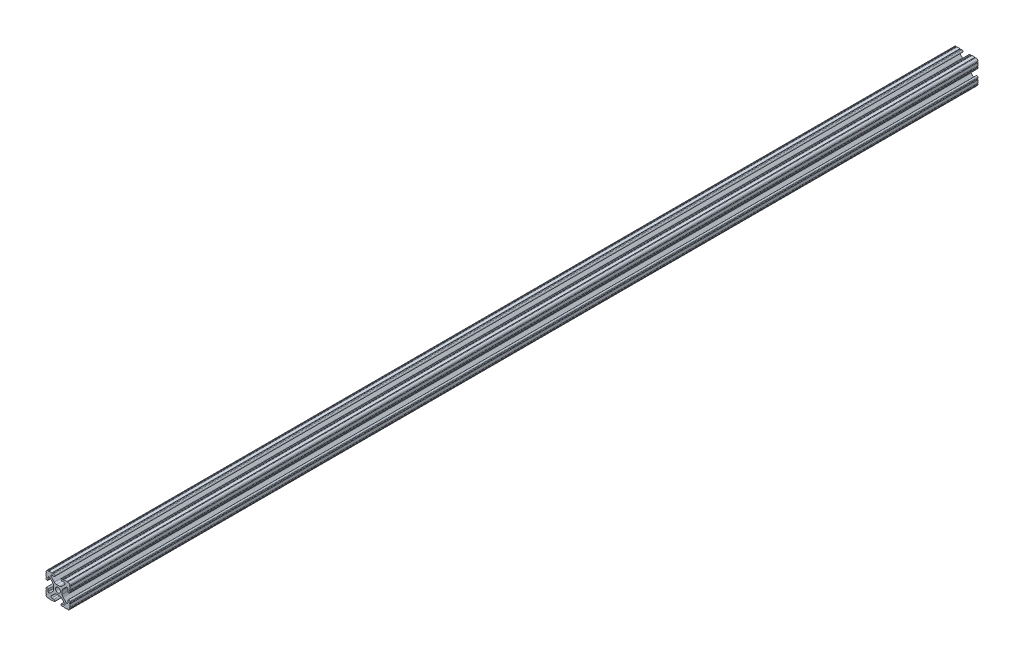
SolidWorks part; units mm, degrees
material "6061-T6 (SS)"
ref_plane "Front Plane" through (0, 0, 0) normal (0, 0, 1) x (1, 0, 0)
ref_plane "Top Plane" through (0, 0, 0) normal (0, 1, 0) x (1, 0, 0)
ref_plane "Right Plane" through (0, 0, 0) normal (1, 0, 0) x (0, 0, -1)
ref_plane "Plane1" through (0, 0, -450.85) normal (0, 0, -1) x (-1, 0, 0)
sketch "Sketch1" plane through (0, 0, -450.85) normal (0, 0, -1) x (-1, 0, 0)
  line L0 (12.7, -9.5504) -> (12.7, -6.3331)
  line L1 (12.7, -5.3171) -> (12.7, -4.3434)
  line L2 (10.4902, -4.3434) -> (10.4902, -6.4748)
  line L3 (8.7558, -7.1932) -> (5.4257, -3.8632)
  line L4 (4.4958, -1.6181) -> (4.4958, 1.6181)
  line L5 (5.4257, 3.8632) -> (8.7558, 7.1932)
  line L6 (10.4902, 6.4748) -> (10.4902, 4.3434)
  line L7 (12.7, 4.3434) -> (12.7, 5.3171)
  line L8 (12.7, 6.3331) -> (12.7, 9.5504)
  line L9 (9.5504, 12.7) -> (6.3331, 12.7)
  line L10 (5.3171, 12.7) -> (4.3434, 12.7)
  line L11 (4.3434, 10.4902) -> (6.4748, 10.4902)
  line L12 (7.1932, 8.7558) -> (3.8632, 5.4257)
  line L13 (1.6181, 4.4958) -> (-1.6181, 4.4958)
  line L14 (-3.8632, 5.4257) -> (-7.1932, 8.7558)
  line L15 (-6.4748, 10.4902) -> (-4.3434, 10.4902)
  line L16 (-4.3434, 12.7) -> (-5.3171, 12.7)
  line L17 (-6.3331, 12.7) -> (-9.5504, 12.7)
  line L18 (-12.7, 9.5504) -> (-12.7, 6.3331)
  line L19 (-12.7, 5.3171) -> (-12.7, 4.3434)
  line L20 (-10.4902, 4.3434) -> (-10.4902, 6.4748)
  line L21 (-8.7558, 7.1932) -> (-5.4257, 3.8632)
  line L22 (-4.4958, 1.6181) -> (-4.4958, -1.6181)
  line L23 (-5.4257, -3.8632) -> (-8.7558, -7.1932)
  line L24 (-10.4902, -6.4748) -> (-10.4902, -4.3434)
  line L25 (-12.7, -4.3434) -> (-12.7, -5.3171)
  line L26 (-12.7, -6.3331) -> (-12.7, -9.5504)
  line L27 (-9.5504, -12.7) -> (-6.3331, -12.7)
  line L28 (-5.3171, -12.7) -> (-4.3434, -12.7)
  line L29 (-4.3434, -10.4902) -> (-6.4748, -10.4902)
  line L30 (-7.1932, -8.7558) -> (-3.8632, -5.4257)
  line L31 (-1.6181, -4.4958) -> (1.6181, -4.4958)
  line L32 (3.8632, -5.4257) -> (7.1932, -8.7558)
  line L33 (6.4748, -10.4902) -> (4.3434, -10.4902)
  line L34 (4.3434, -12.7) -> (5.3171, -12.7)
  line L35 (6.3331, -12.7) -> (9.5504, -12.7)
  arc A0 (12.6998, -10.5664) -> (12.7, -9.5504) centre (12.7, -10.0584) cw
  arc A1 (12.7, -6.3331) -> (12.7, -5.3171) centre (12.7, -5.8251) cw
  arc A2 (12.7, -4.3434) -> (10.4902, -4.3434) centre (11.5951, -4.3434) ccw
  arc A3 (10.4902, -6.4748) -> (8.7558, -7.1932) centre (9.4742, -6.4748) cw
  arc A4 (5.4257, -3.8632) -> (4.4958, -1.6181) centre (7.6708, -1.6181) cw
  arc A5 (4.4958, 1.6181) -> (5.4257, 3.8632) centre (7.6708, 1.6181) cw
  arc A6 (8.7558, 7.1932) -> (10.4902, 6.4748) centre (9.4742, 6.4748) cw
  arc A7 (10.4902, 4.3434) -> (12.7, 4.3434) centre (11.5951, 4.3434) ccw
  arc A8 (12.7, 5.3171) -> (12.7, 6.3331) centre (12.7, 5.8251) cw
  arc A9 (12.7, 9.5504) -> (12.6998, 10.5664) centre (12.7, 10.0584) cw
  arc A10 (12.6998, 10.5664) -> (10.5664, 12.6998) centre (10.5918, 10.5918) ccw
  arc A11 (10.5664, 12.6998) -> (9.5504, 12.7) centre (10.0584, 12.7) cw
  arc A12 (6.3331, 12.7) -> (5.3171, 12.7) centre (5.8251, 12.7) cw
  arc A13 (4.3434, 12.7) -> (4.3434, 10.4902) centre (4.3434, 11.5951) ccw
  arc A14 (6.4748, 10.4902) -> (7.1932, 8.7558) centre (6.4748, 9.4742) cw
  arc A15 (3.8632, 5.4257) -> (1.6181, 4.4958) centre (1.6181, 7.6708) cw
  arc A16 (-1.6181, 4.4958) -> (-3.8632, 5.4257) centre (-1.6181, 7.6708) cw
  arc A17 (-7.1932, 8.7558) -> (-6.4748, 10.4902) centre (-6.4748, 9.4742) cw
  arc A18 (-4.3434, 10.4902) -> (-4.3434, 12.7) centre (-4.3434, 11.5951) ccw
  arc A19 (-5.3171, 12.7) -> (-6.3331, 12.7) centre (-5.8251, 12.7) cw
  arc A20 (-9.5504, 12.7) -> (-10.5664, 12.6998) centre (-10.0584, 12.7) cw
  arc A21 (-10.5664, 12.6998) -> (-12.6998, 10.5664) centre (-10.5918, 10.5918) ccw
  arc A22 (-12.6998, 10.5664) -> (-12.7, 9.5504) centre (-12.7, 10.0584) cw
  arc A23 (-12.7, 6.3331) -> (-12.7, 5.3171) centre (-12.7, 5.8251) cw
  arc A24 (-12.7, 4.3434) -> (-10.4902, 4.3434) centre (-11.5951, 4.3434) ccw
  arc A25 (-10.4902, 6.4748) -> (-8.7558, 7.1932) centre (-9.4742, 6.4748) cw
  arc A26 (-5.4257, 3.8632) -> (-4.4958, 1.6181) centre (-7.6708, 1.6181) cw
  arc A27 (-4.4958, -1.6181) -> (-5.4257, -3.8632) centre (-7.6708, -1.6181) cw
  arc A28 (-8.7558, -7.1932) -> (-10.4902, -6.4748) centre (-9.4742, -6.4748) cw
  arc A29 (-10.4902, -4.3434) -> (-12.7, -4.3434) centre (-11.5951, -4.3434) ccw
  arc A30 (-12.7, -5.3171) -> (-12.7, -6.3331) centre (-12.7, -5.8251) cw
  arc A31 (-12.7, -9.5504) -> (-12.6998, -10.5664) centre (-12.7, -10.0584) cw
  arc A32 (-12.6998, -10.5664) -> (-10.5664, -12.6998) centre (-10.5918, -10.5918) ccw
  arc A33 (-10.5664, -12.6998) -> (-9.5504, -12.7) centre (-10.0584, -12.7) cw
  arc A34 (-6.3331, -12.7) -> (-5.3171, -12.7) centre (-5.8251, -12.7) cw
  arc A35 (-4.3434, -12.7) -> (-4.3434, -10.4902) centre (-4.3434, -11.5951) ccw
  arc A36 (-6.4748, -10.4902) -> (-7.1932, -8.7558) centre (-6.4748, -9.4742) cw
  arc A37 (-3.8632, -5.4257) -> (-1.6181, -4.4958) centre (-1.6181, -7.6708) cw
  arc A38 (1.6181, -4.4958) -> (3.8632, -5.4257) centre (1.6181, -7.6708) cw
  arc A39 (7.1932, -8.7558) -> (6.4748, -10.4902) centre (6.4748, -9.4742) cw
  arc A40 (4.3434, -10.4902) -> (4.3434, -12.7) centre (4.3434, -11.5951) ccw
  arc A41 (5.3171, -12.7) -> (6.3331, -12.7) centre (5.8251, -12.7) cw
  arc A42 (9.5504, -12.7) -> (10.5664, -12.6998) centre (10.0584, -12.7) cw
  arc A43 (10.5664, -12.6998) -> (12.6998, -10.5664) centre (10.5918, -10.5918) ccw
  circle A44 centre (0, 0) radius 2.6035
extrude "Boss-Extrude1" add sketch "Sketch1" against normal blind 965.2
